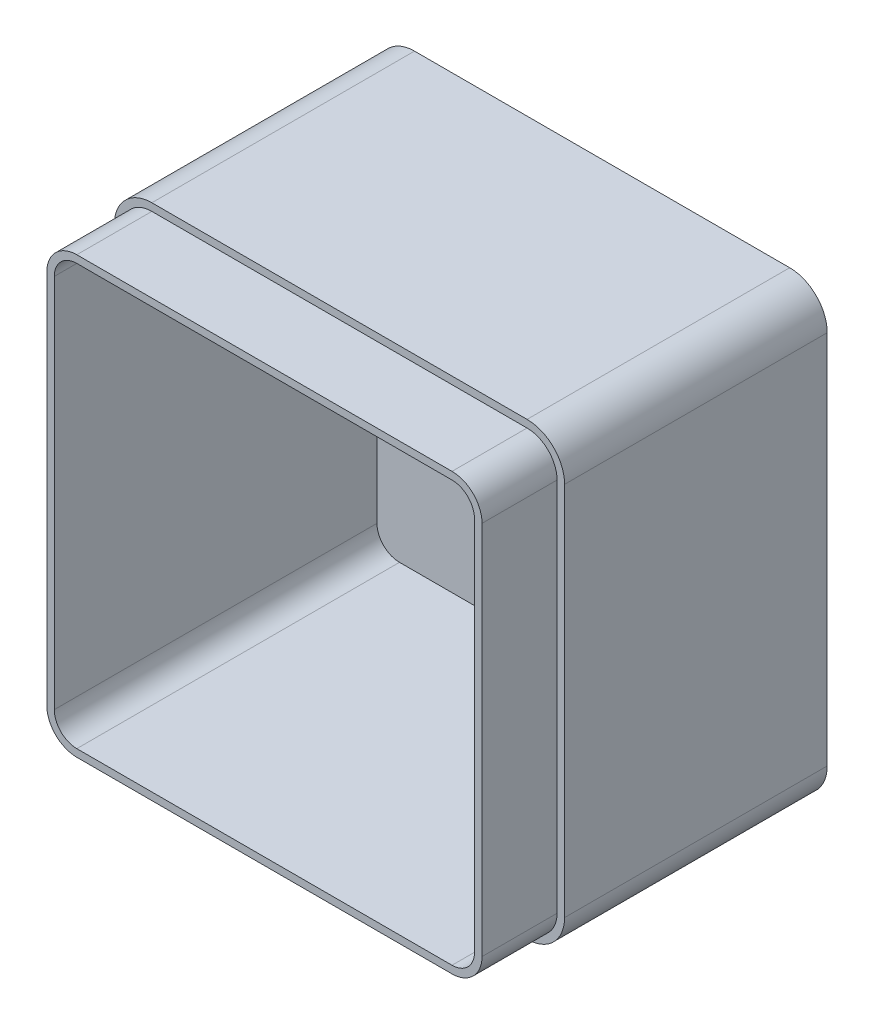
SolidWorks part; units mm, degrees
ref_plane "Front" through (0, 0, 0) normal (0, 0, 1) x (1, 0, 0)
ref_plane "Top" through (0, 0, 0) normal (0, 1, 0) x (1, 0, 0)
ref_plane "Right" through (0, 0, 0) normal (1, 0, 0) x (0, 0, -1)
sketch "Sketch1" plane through (0, 0, 0) normal (0, 0, 1) x (1, 0, 0)
  line L1 (0, 0) -> (120, 0)
  line L2 (0, 0) -> (0, 120)
  line L3 (0, 120) -> (120, 120)
  line L4 (120, 0) -> (120, 120)
  dimension "D1" = 120
  dimension "D2" = 120
extrude "Boss-Extrude1" add sketch "Sketch1" along normal blind 90
fillet "Fillet1" radius 10 4 edges at (0, 0, 45) (120, 0, 45) (120, 120, 45) (0, 120, 45)
shell "Shell1" thickness 4
sketch "Sketch2" plane through (0, 0, 90) normal (0, 0, 1) x (1, 0, 0)
  line L0 (2, 110) -> (2, 10)
  line L1 (10, 2) -> (110, 2)
  line L2 (118, 10) -> (118, 110)
  line L3 (110, 118) -> (10, 118)
  line L4 (0, 110) -> (0, 10)
  line L5 (10, 0) -> (110, 0)
  line L6 (120, 10) -> (120, 110)
  line L7 (110, 120) -> (10, 120)
  line L8 (0, 110) -> (0, 10)
  line L9 (10, 0) -> (110, 0)
  line L10 (120, 10) -> (120, 110)
  line L11 (110, 120) -> (10, 120)
  arc A0 (2, 10) -> (10, 2) centre (10, 10) ccw
  arc A1 (110, 2) -> (118, 10) centre (110, 10) ccw
  arc A2 (118, 110) -> (110, 118) centre (110, 110) ccw
  arc A3 (10, 118) -> (2, 110) centre (10, 110) ccw
  arc A4 (0, 10) -> (10, 0) centre (10, 10) ccw
  arc A5 (110, 0) -> (120, 10) centre (110, 10) ccw
  arc A6 (120, 110) -> (110, 120) centre (110, 110) ccw
  arc A7 (10, 120) -> (0, 110) centre (10, 110) ccw
  arc A8 (0, 10) -> (10, 0) centre (10, 10) ccw
  arc A9 (110, 0) -> (120, 10) centre (110, 10) ccw
  arc A10 (120, 110) -> (110, 120) centre (110, 110) ccw
  arc A11 (10, 120) -> (0, 110) centre (10, 110) ccw
  dimension "D1" = 0
  dimension "D2" = 2
extrude "Cut-Extrude1" cut sketch "Sketch2" against normal blind 20
